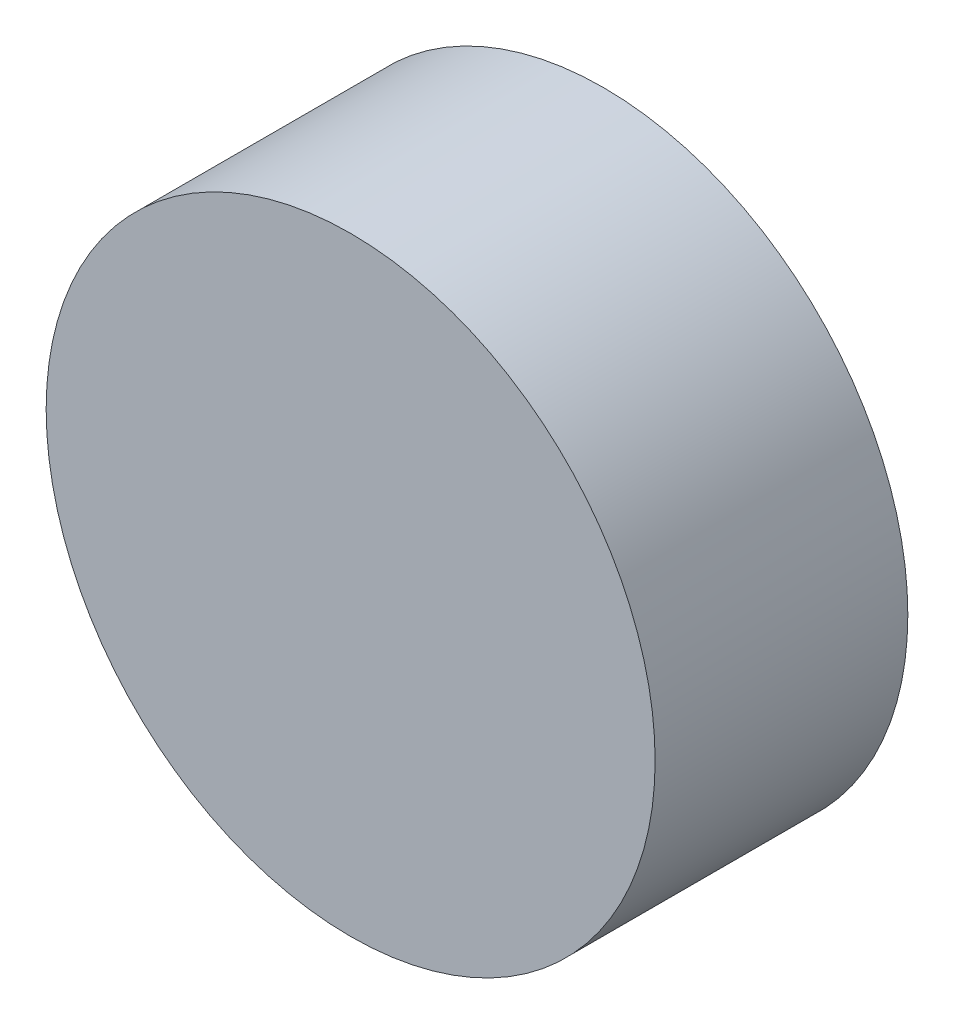
SolidWorks part; units mm, degrees
ref_plane "Front Plane" through (0, 0, 0) normal (0, 0, 1) x (1, 0, 0)
ref_plane "Top Plane" through (0, 0, 0) normal (0, 1, 0) x (1, 0, 0)
ref_plane "Right Plane" through (0, 0, 0) normal (1, 0, 0) x (0, 0, -1)
sketch "Sketch1" plane through (0, 0, 0) normal (0, 0, 1) x (1, 0, 0)
  circle A0 centre (0, 0) radius 234.95
  dimension "D1" = 469.9
extrude "Boss-Extrude1" add sketch "Sketch1" against normal blind 195
